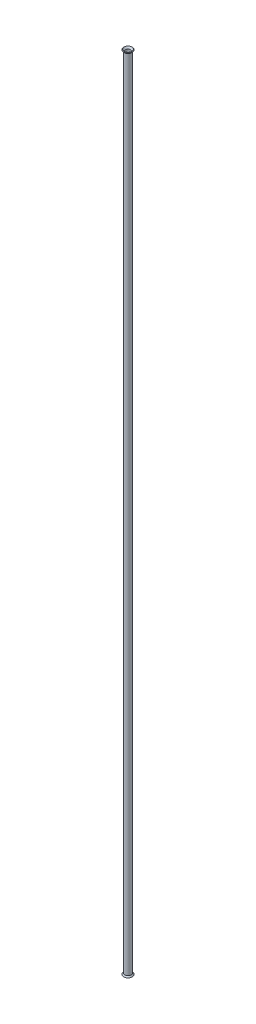
SolidWorks part; units mm, degrees
material "6061-T6 (SS)"
ref_plane "Front Plane" through (0, 0, 0) normal (0, 0, 1) x (1, 0, 0)
ref_plane "Top Plane" through (0, 0, 0) normal (0, 1, 0) x (1, 0, 0)
ref_plane "Right Plane" through (0, 0, 0) normal (1, 0, 0) x (0, 0, -1)
sketch "Sketch1" plane through (0, 0, 0) normal (0, 1, 0) x (1, 0, 0)
  circle A0 centre (0, 0) radius 9.525
  circle A1 centre (0, 0) radius 12.7
  dimension "D1" = 25.4
  dimension "D2" = 19.05
extrude "Boss-Extrude1" add sketch "Sketch1" along normal blind 3093.72 contours A1
ref_axis "Axis1" through (0, 3248.406, 0) along (0, -1, 0)
sketch "Sketch2" plane through (0, 0, 0) normal (0, 0, 1) x (1, 0, 0)
  line L0 (12.7, 3093.72) -> (21.0864, 3093.72) construction
  line L1 (12.7, 3093.72) -> (-12.7, 3093.72) construction
  line L2 (12.7, 3093.72) -> (16.7817, 3098.5844)
  line L3 (9.525, 3093.72) -> (14.9185, 3100.1478)
  line L4 (9.525, 3093.72) -> (-9.525, 3093.72) construction
  line L5 (16.7817, 3098.5844) -> (14.9185, 3100.1478)
  line L6 (12.7, 3093.72) -> (9.525, 3093.72)
  dimension "D1" = 50
  dimension "D2" = 6.35
  dimension "D3" = 2.4322
  dimension "D4" = 9.525
revolve "Revolve1" add sketch "Sketch2" angle 360 about axis through (0, 3248.406, 0) along (0, -1, 0)
ref_plane "Plane1" through (0, 1546.86, 0) normal (0, 1, 0) x (1, 0, 0)
mirror "Mirror1" about plane through (0, 1546.86, 0) normal (0, 1, 0) of "Revolve1"
